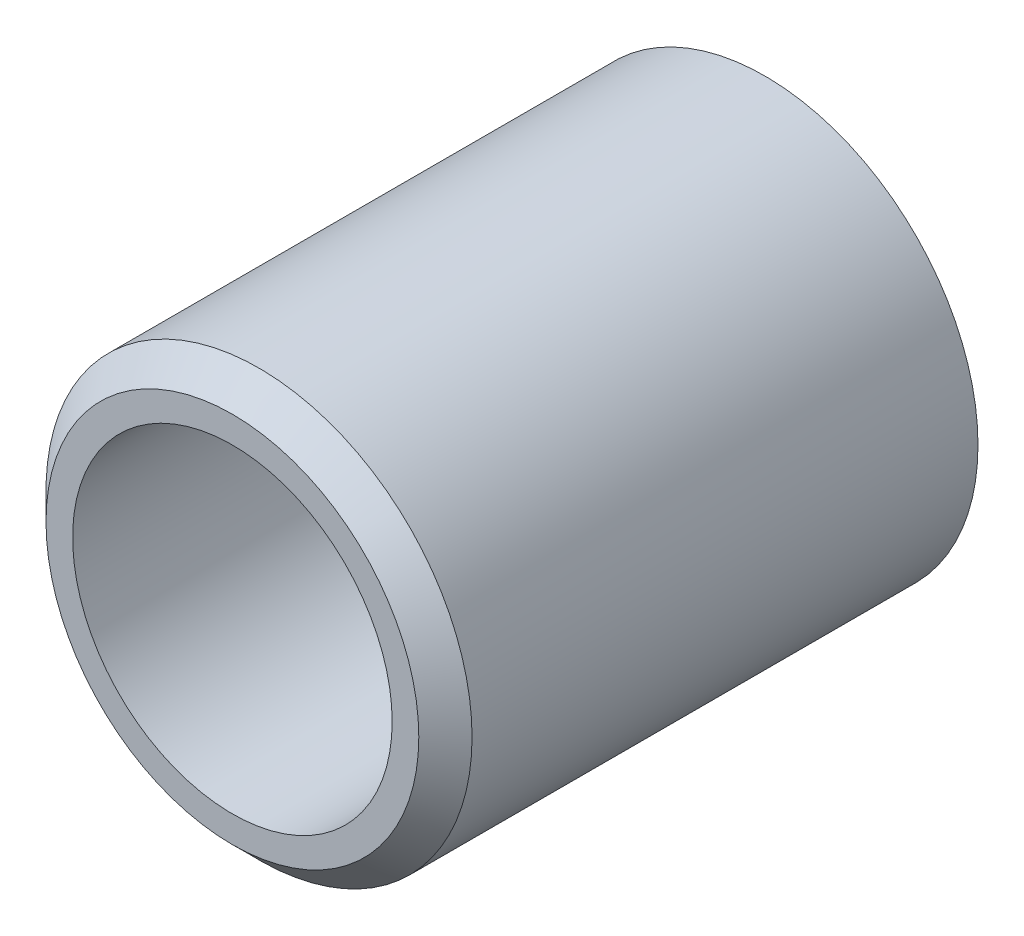
SolidWorks part; units mm, degrees
ref_plane "前基準面" through (0, 0, 0) normal (0, 0, 1) x (1, 0, 0)
ref_plane "上基準面" through (0, 0, 0) normal (0, 1, 0) x (1, 0, 0)
ref_plane "右基準面" through (0, 0, 0) normal (1, 0, 0) x (0, 0, -1)
sketch "草圖2" plane through (0, 0, 0) normal (1, 0, 0) x (0, 0, -1)
  line L0 (-9.4369, 0) -> (8.4685, 0) construction
  line L1 (0, 0) -> (0, 3.5) construction
  line L2 (0.5, 4) -> (10, 4)
  line L3 (10, 4) -> (10, 0) construction
  line L4 (0, 3.5) -> (0.5, 4)
  line L5 (0, 3.5) -> (0, 3)
  line L6 (0, 3) -> (9.5, 3)
  line L7 (10, 3.5) -> (10, 4)
  line L8 (9.5, 3) -> (10, 3.5)
  point P4 (0, 4)
  point P7 (10, 3)
  dimension "D1" = 10
  dimension "D2" = 8
  dimension "D3" = 6
revolve "旋轉1" add sketch "草圖2" angle 360 about L0
